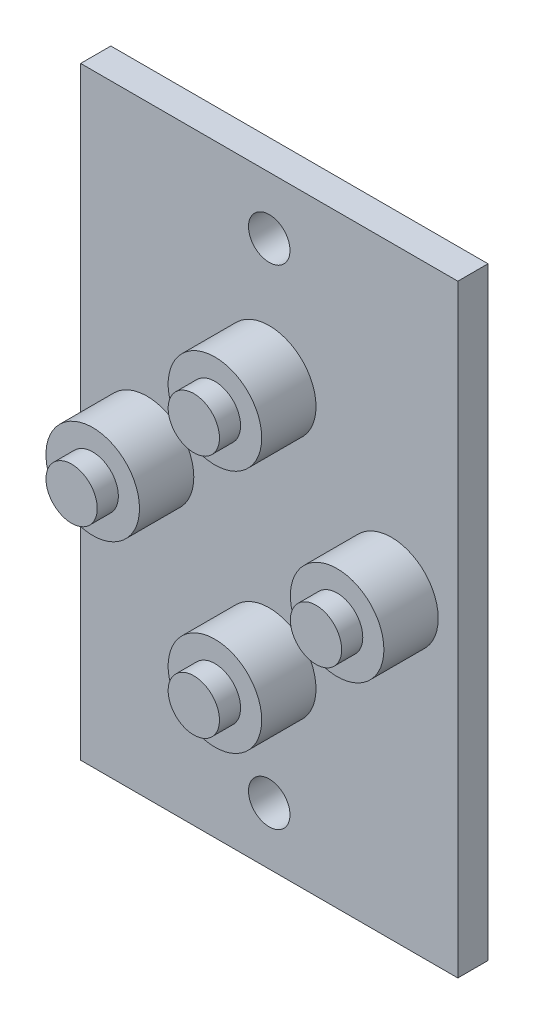
SolidWorks part; units mm, degrees
ref_plane "Front Plane" through (0, 0, 0) normal (0, 0, 1) x (1, 0, 0)
ref_plane "Top Plane" through (0, 0, 0) normal (0, 1, 0) x (1, 0, 0)
ref_plane "Right Plane" through (0, 0, 0) normal (1, 0, 0) x (0, 0, -1)
sketch "Sketch1" plane through (0, 0, 0) normal (0, 0, 1) x (1, 0, 0)
  line L1 (-12.5, 20) -> (12.5, 20)
  line L2 (-12.5, 20) -> (-12.5, -20)
  line L3 (-12.5, -20) -> (12.5, -20)
  line L4 (12.5, 20) -> (12.5, -20)
  line L5 (-12.5, 20) -> (12.5, -20) construction
  line L6 (-12.5, -20) -> (12.5, 20) construction
  point P0 (0, 0)
  dimension "D1" = 40
  dimension "D2" = 25
extrude "Boss-Extrude1" add sketch "Sketch1" along normal blind 2
sketch "Sketch2" plane through (0, 0, 2) normal (0, 0, 1) x (1, 0, 0)
  circle A0 centre (-8.1, 0) radius 3.1
  circle A1 centre (8.1, 0) radius 3.1
  circle A2 centre (0, 8.1) radius 3.1
  circle A3 centre (0, -8.1) radius 3.1
  dimension "D1" = 6.2
  dimension "D2" = 8.1
  dimension "D3" = 6.2
  dimension "D4" = 8.1
  dimension "D5" = 6.2
  dimension "D6" = 6.2
  dimension "D8" = 8.1
  dimension "D9" = 8.1
  dimension "D10" = 8.1
  dimension "D11" = 8.1
  dimension "D12" = 8.1
  dimension "D7" = 8.1
extrude "Boss-Extrude2" add sketch "Sketch2" along normal blind 3.6
sketch "Sketch3" plane through (0, 0, 5.6) normal (0, 0, 1) x (1, 0, 0)
  circle A0 centre (0, 8.1) radius 1.7
  dimension "D1" = 3.4
extrude "Boss-Extrude3" add sketch "Sketch3" along normal blind 1.4
sketch "Sketch4" plane through (0, 0, 5.6) normal (0, 0, 1) x (1, 0, 0)
  circle A0 centre (-8.1, 0) radius 1.7
  dimension "D1" = 3.4
extrude "Boss-Extrude4" add sketch "Sketch4" along normal blind 1.4
sketch "Sketch5" plane through (0, 0, 5.6) normal (0, 0, 1) x (1, 0, 0)
  circle A0 centre (8.1, 0) radius 1.7
  dimension "D1" = 3.4
extrude "Boss-Extrude5" add sketch "Sketch5" along normal blind 1.4
sketch "Sketch6" plane through (0, 0, 5.6) normal (0, 0, 1) x (1, 0, 0)
  circle A0 centre (0, -8.1) radius 1.7
  dimension "D1" = 3.4
extrude "Boss-Extrude6" add sketch "Sketch6" along normal blind 1.4
sketch "Sketch7" plane through (0, 0, 2) normal (0, 0, 1) x (1, 0, 0)
  circle A0 centre (0, 16.2) radius 1.375
  circle A1 centre (0, -16.2) radius 1.375
  circle A2 centre (0, 8.1) radius 1.7 construction
  circle A3 centre (0, -8.1) radius 1.7 construction
  dimension "D1" = 2.75
  dimension "D2" = 2.75
  dimension "D3" = 8.1
  dimension "D4" = 8.1
extrude "Cut-Extrude1" cut sketch "Sketch7" against normal blind 3
